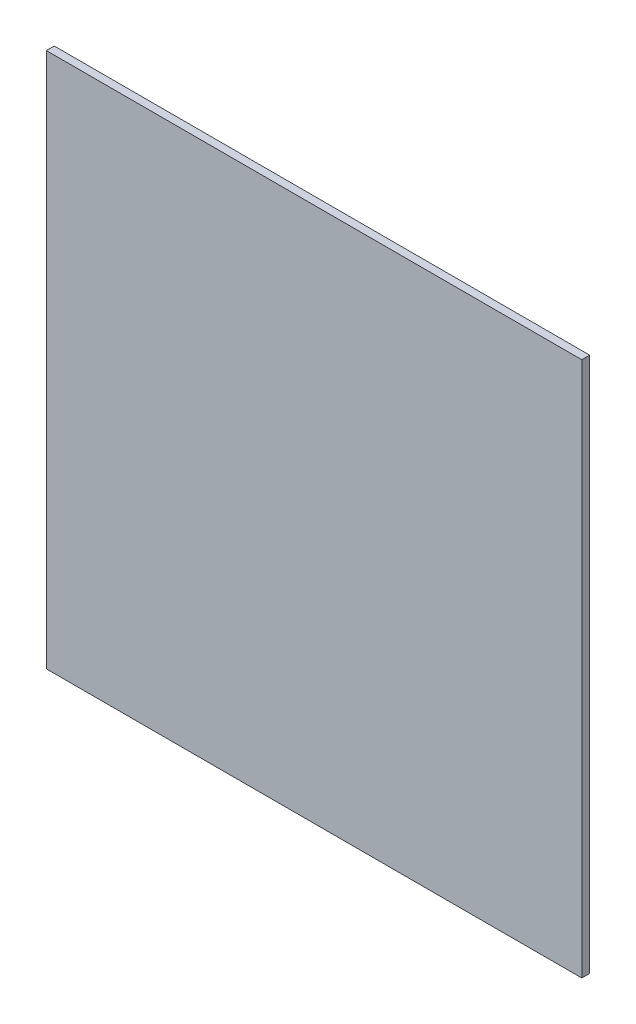
SolidWorks part; units mm, degrees
material "Pine"
ref_plane "Front Plane" through (0, 0, 0) normal (0, 0, 1) x (1, 0, 0)
ref_plane "Top Plane" through (0, 0, 0) normal (0, 1, 0) x (1, 0, 0)
ref_plane "Right Plane" through (0, 0, 0) normal (1, 0, 0) x (0, 0, -1)
sketch "Sketch1" plane through (0, 0, 0) normal (0, 0, 1) x (1, 0, 0)
  line L1 (610, -610) -> (-610, -610)
  line L2 (610, -610) -> (610, 610)
  line L3 (610, 610) -> (-610, 610)
  line L4 (-610, -610) -> (-610, 610)
  line L5 (610, -610) -> (-610, 610) construction
  line L6 (610, 610) -> (-610, -610) construction
  point P0 (0, 0)
  dimension "D1" = 1220
extrude "Boss-Extrude1" add sketch "Sketch1" against normal blind 18 from offset 8
